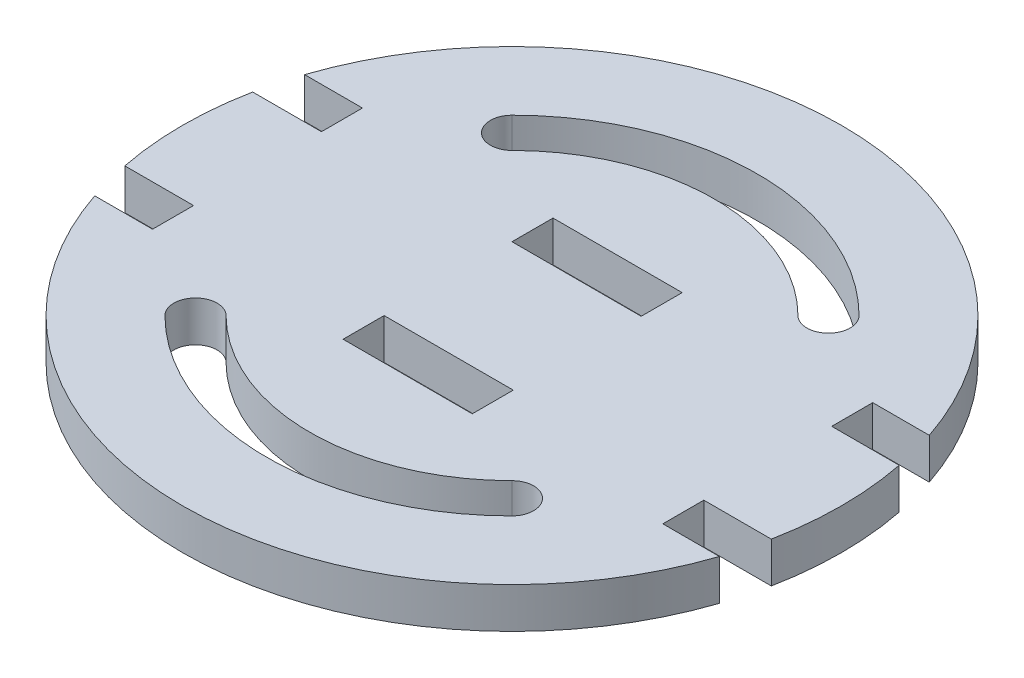
SolidWorks part; units mm, degrees
ref_plane "Front" through (0, 0, 0) normal (0, 0, 1) x (1, 0, 0)
ref_plane "Top" through (0, 0, 0) normal (0, 1, 0) x (1, 0, 0)
ref_plane "Right" through (0, 0, 0) normal (1, 0, 0) x (0, 0, -1)
sketch "Sketch1" plane through (0, 0, 0) normal (0, 1, 0) x (1, 0, 0)
  line L0 (-48.8466, 16.4135) -> (-39.8, 16.4135)
  line L1 (-39.8, 16.4135) -> (-39.8, 10)
  line L2 (-39.8, 10) -> (-50.5509, 10)
  line L3 (-10, 16.4135) -> (-10, 10)
  line L4 (-10, 10) -> (10.2, 10)
  line L5 (10.2, 10) -> (10.2, 16.4135)
  line L6 (10.2, 16.4135) -> (-10, 16.4135)
  line L7 (48.8466, 16.4135) -> (40, 16.4135)
  line L8 (40, 16.4135) -> (40, 10)
  line L9 (40, 10) -> (50.5509, 10)
  line L10 (-51.5305, 0) -> (51.5305, 0) construction
  line L11 (40, -10) -> (50.5509, -10)
  line L12 (40, -16.4135) -> (40, -10)
  line L13 (48.8466, -16.4135) -> (40, -16.4135)
  line L14 (10.2, -16.4135) -> (-10, -16.4135)
  line L15 (10.2, -10) -> (10.2, -16.4135)
  line L16 (-10, -10) -> (10.2, -10)
  line L17 (-10, -16.4135) -> (-10, -10)
  line L18 (-39.8, -10) -> (-50.5509, -10)
  line L19 (-39.8, -16.4135) -> (-39.8, -10)
  line L20 (-48.8466, -16.4135) -> (-39.8, -16.4135)
  circle A0 centre (0, 0) radius 51.5305
  dimension "D1" = 103.061
  dimension "D2" = 6.4135
  dimension "D3" = 6.4135
  dimension "D4" = 6.4135
  dimension "D5" = 20.2
  dimension "D6" = 10
  dimension "D7" = 10
  dimension "D8" = 10
  dimension "D9" = 29.8
  dimension "D10" = 29.8
extrude "Boss-Extrude1" add sketch "Sketch1" along normal blind 6.35 contours A0 L10 L9 L8 L7 L0 L1 L2 L6 L5 L4 L3 | L10 A0 L18 L19 L20 L13 L12 L11 L14 L17 L16 L15
sketch "Sketch2" plane through (0, 6.35, 0) normal (0, 1, 0) x (1, 0, 0)
  line L0 (-0.0815, -0.0815) -> (46.5744, 46.5744) construction
  line L1 (0.0074, -0.0074) -> (-43.5573, 43.5573) construction
  line L2 (0, 0) -> (34.5448, 0) construction
  arc A0 (-24.7487, -24.7487) -> (24.7487, -24.7487) centre (0, 0) ccw construction
  arc A1 (-27.1375, -27.1375) -> (27.1375, -27.1375) centre (0, 0) ccw
  arc A2 (-22.36, -22.36) -> (22.36, -22.36) centre (0, 0) ccw
  arc A3 (-22.36, -22.36) -> (-27.1375, -27.1375) centre (-24.7487, -24.7487) ccw
  arc A4 (27.1375, -27.1375) -> (22.36, -22.36) centre (24.7487, -24.7487) ccw
  arc A5 (-24.7487, 24.7487) -> (24.7487, 24.7487) centre (0, 0) cw construction
  arc A6 (-27.1375, 27.1375) -> (27.1375, 27.1375) centre (0, 0) cw
  arc A7 (-22.36, 22.36) -> (22.36, 22.36) centre (0, 0) cw
  arc A8 (-22.36, 22.36) -> (-27.1375, 27.1375) centre (-24.7487, 24.7487) cw
  arc A9 (27.1375, 27.1375) -> (22.36, 22.36) centre (24.7487, 24.7487) cw
  point P4 (0, -35)
  point P17 (0, 35)
  dimension "D4" = 6.7564
  dimension "D1" = 35
  dimension "D2" = 90
  dimension "D3" = 45
extrude "Cut-Extrude1" cut sketch "Sketch2" against normal through all
